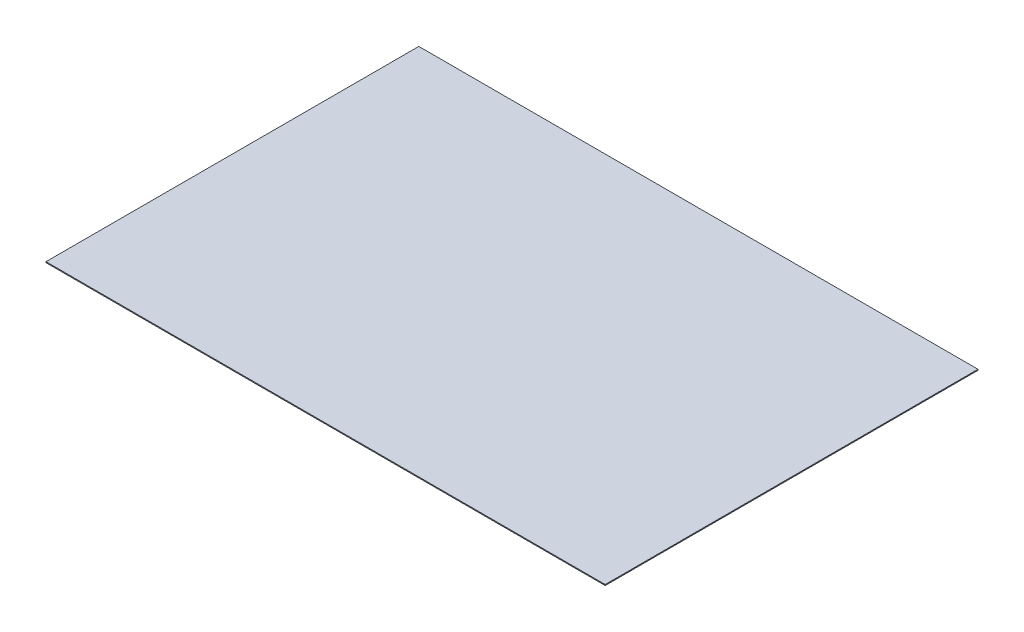
SolidWorks part; units mm, degrees
ref_plane "Front Plane" through (0, 0, 0) normal (0, 0, 1) x (1, 0, 0)
ref_plane "Top Plane" through (0, 0, 0) normal (0, 1, 0) x (1, 0, 0)
ref_plane "Right Plane" through (0, 0, 0) normal (1, 0, 0) x (0, 0, -1)
sketch "Sketch1" plane through (0, 0, 0) normal (0, 0, 1) x (1, 0, 0)
  line L0 (-228.6, 0) -> (228.6, 0) construction
  line L1 (0, -0.381) -> (0, 0.381) construction
  point P5 (0, 0)
  point P9 (0, 0)
  dimension "Width" = 457.2
  dimension "Thickness" = 0.762
sketch "Sketch2" plane through (0, 0, 0) normal (1, 0, 0) x (0, 0, -1)
  line L0 (-152.4, 0) -> (152.4, 0) construction
  point P3 (0, 0)
  dimension "Length" = 304.8
sketch "Sketch3" plane through (0, 0, 0) normal (0, 0, 1) x (1, 0, 0)
  line L1 (-228.6, -0.381) -> (228.6, -0.381)
  line L2 (-228.6, -0.381) -> (-228.6, 0.381)
  line L3 (-228.6, 0.381) -> (228.6, 0.381)
  line L4 (228.6, -0.381) -> (228.6, 0.381)
  line L5 (-228.6, -0.381) -> (228.6, 0.381) construction
  line L6 (-228.6, 0.381) -> (228.6, -0.381) construction
  point P0 (0, 0)
extrude "Boss-Extrude1" add sketch "Sketch3" along normal mid plane 304.8
sketch "Sketch4" plane through (0, 0, 0) normal (0, 1, 0) x (1, 0, 0)
  line L0 (-228.6, 0) -> (-112.7252, 0)
  line L1 (112.7252, 0) -> (228.6, 0)
  line L2 (0, 152.4) -> (0, 36.5252)
  line L3 (0, -36.5252) -> (0, -152.4)
  point P6 (228.6, -152.4)
  point P9 (-228.6, 152.4)
  point P10 (-112.7252, 0)
  point P11 (0, -36.5252)
  point P12 (112.7252, 0)
  point P13 (228.6, 152.4)
  point P22 (0, 36.5252)
  dimension "D1" = 115.8748
sketch "Sketch5" plane through (0, 0, 0) normal (1, 0, 0) x (0, 0, -1)
  point P0 (152.4, 0.381)
  point P1 (152.4, -0.381)
equation "\"D1@Boss-Extrude1\"=\"Length@Sketch2\""
